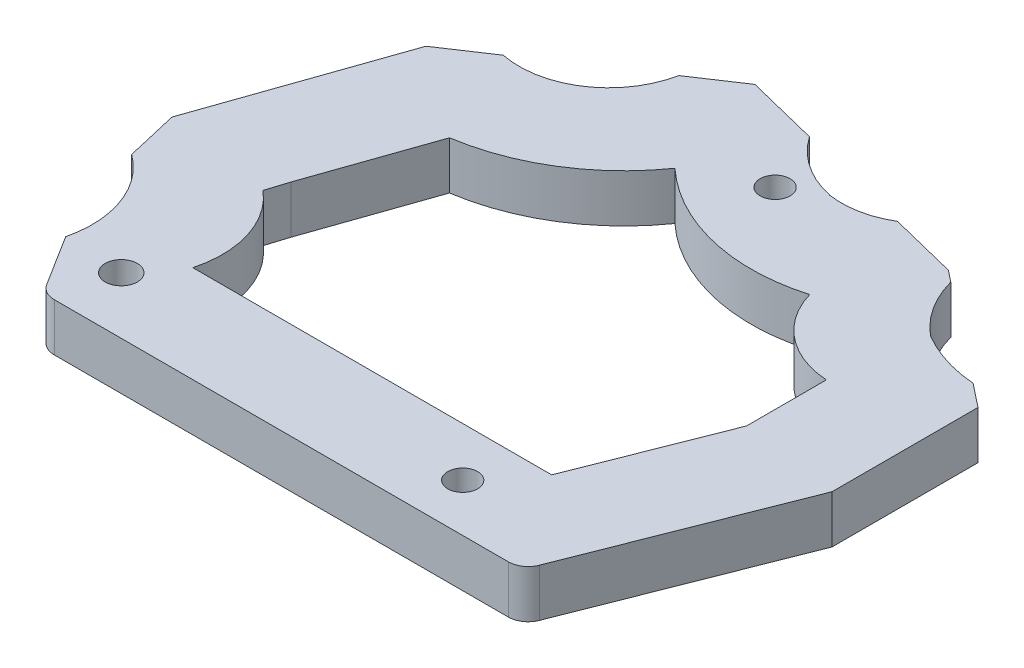
SolidWorks part; units mm, degrees
ref_plane "Front Plane" through (0, 0, 0) normal (0, 0, 1) x (1, 0, 0)
ref_plane "Top Plane" through (0, 0, 0) normal (0, 1, 0) x (1, 0, 0)
ref_plane "Right Plane" through (0, 0, 0) normal (1, 0, 0) x (0, 0, -1)
sketch "Sketch1" plane through (0, 0, 0) normal (0, 1, 0) x (1, 0, 0)
  line L0 (-1.9462, 28.697) -> (58.3998, 28.697) construction
  line L1 (5.2688, 9.726) -> (41.2688, 9.726)
  line L3 (6.8647, 33.8793) -> (2.7512, 22.0756)
  line L4 (46.7889, 31.7527) -> (46.7889, 23.7527)
  line L5 (46.7889, 23.7527) -> (41.2688, 9.726)
  line L6 (-7.6262, 16.494) -> (-8.8505, 21.7626)
  line L7 (-8.8505, 21.7626) -> (-2.269, 40.6486)
  line L9 (-3.789, 6.0409) -> (0, 0)
  line L10 (0, 0) -> (48, 0)
  line L19 (-2.269, 40.6486) -> (2.3865, 43.7457)
  line L20 (6.8647, 33.8793) -> (1.5475, 41.1573)
  line L26 (17.5457, 53.8305) -> (24.8242, 52.0214)
  line L34 (56.7889, 36.9597) -> (54.4348, 38.8193)
  line L35 (12.9665, 50.7841) -> (17.5457, 53.8305)
  line L38 (43.3866, 47.3955) -> (44.5342, 46.4831)
  line L40 (36.594, 49.087) -> (43.3866, 47.3955)
  line L41 (56.7889, 36.9597) -> (56.7889, 22.3328)
  line L42 (56.7889, 22.3328) -> (48, 0)
  line L43 (2.7512, 22.0756) -> (2.0857, 19.9526)
  arc A1 (6.8647, 33.8793) -> (20.8176, 42.5344) centre (3.6857, 54.5784) ccw
  arc A7 (-7.6262, 16.494) -> (-3.789, 6.0409) centre (-13.5055, 8.4049) cw
  arc A12 (48.2153, 40.7749) -> (54.4348, 38.8193) centre (55.5185, 53.1336) ccw
  arc A14 (2.3865, 43.7457) -> (12.9665, 50.7841) centre (4.1572, 52.5549) ccw
  arc A15 (24.8242, 52.0214) -> (30.9371, 47.9518) centre (33.036, 57.7304) ccw
  arc A16 (44.5342, 46.4831) -> (48.2153, 40.7749) centre (55.2721, 49.3668) ccw
  arc A17 (20.8176, 42.5344) -> (38.5441, 38.3237) centre (33.4045, 56.1053) ccw
  arc A18 (30.9371, 47.9518) -> (36.594, 49.087) centre (32.1763, 56.4391) ccw
  arc A21 (38.5441, 38.3237) -> (46.7889, 31.7527) centre (47.3283, 40.8875) ccw
  arc A22 (2.0857, 19.9526) -> (5.2688, 9.726) centre (-4.2991, 12.3565) cw
  point P14 (-4.118, 11.8509)
  point P16 (9.1342, 45.0737)
  point P36 (14.7247, 36.7824)
  dimension "D9" = 7.5
  dimension "D1" = 48
  dimension "D2" = 36
  dimension "D3" = 8
  dimension "D4" = 5.5
  dimension "D5" = 20
  dimension "D6" = 12.5
  dimension "D7" = 9.726
  dimension "D8" = 15.0738
  dimension "D10" = 24
  dimension "D11" = 10
  dimension "D12" = 10
  dimension "D13" = 3
  dimension "D14" = 7
  dimension "D15" = 1.4661
  dimension "D16" = 5.5915
extrude "Boss-Extrude1" add sketch "Sketch1" along normal blind 4.8
fillet "Fillet1" radius 2 2 edges at (0, 2.4, 0) (48, 2.4, 0)
sketch "Sketch2" plane through (0, 4.8, 0) normal (0, 1, 0) x (1, 0, 0)
  line L0 (27.4936, 49.4053) -> (27.4936, 45.9053)
  line L1 (2.1248, 0) -> (2.1248, 5.7)
  line L2 (1.1064, 0) -> (46.6378, 0) construction
  line L3 (2.1248, 5.7) -> (-3.5752, 5.7)
  line L4 (-3.789, 6.0409) -> (-0.5879, 0.9373) construction
  arc A0 (24.8242, 52.0214) -> (30.9371, 47.9518) centre (33.036, 57.7304) ccw construction
  circle A1 centre (27.4936, 45.9053) radius 1.5
  circle A2 centre (2.1248, 5.7) radius 1.6147
  circle A3 centre (37.2688, 4.8) radius 1.5
  dimension "D2" = 3
  dimension "D5" = 3
  dimension "D1" = 3.5
  dimension "D3" = 5.7
  dimension "D4" = 5.7
  dimension "D6" = 4.8
  dimension "D7" = 4
extrude "Cut-Extrude1" cut sketch "Sketch2" against normal blind 10
